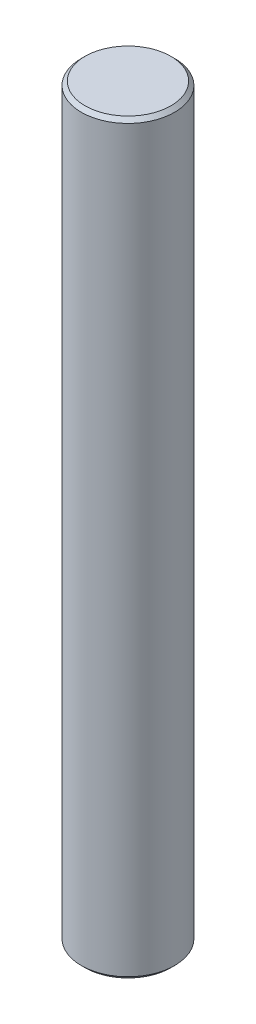
SolidWorks part; units mm, degrees
ref_plane "Front Plane" through (0, 0, 0) normal (0, 0, 1) x (1, 0, 0)
ref_plane "Top Plane" through (0, 0, 0) normal (0, 1, 0) x (1, 0, 0)
ref_plane "Right Plane" through (0, 0, 0) normal (1, 0, 0) x (0, 0, -1)
sketch "Sketch1" plane through (0, 0, 0) normal (0, 1, 0) x (1, 0, 0)
  circle A0 centre (0, 0) radius 12.5
  dimension "D1" = 25
extrude "Boss-Extrude1" add sketch "Sketch1" along normal blind 200
chamfer "Chamfer1" distance 1 angle 45 2 edges at (0, 0, 12.5) (0, 200, 12.5)
